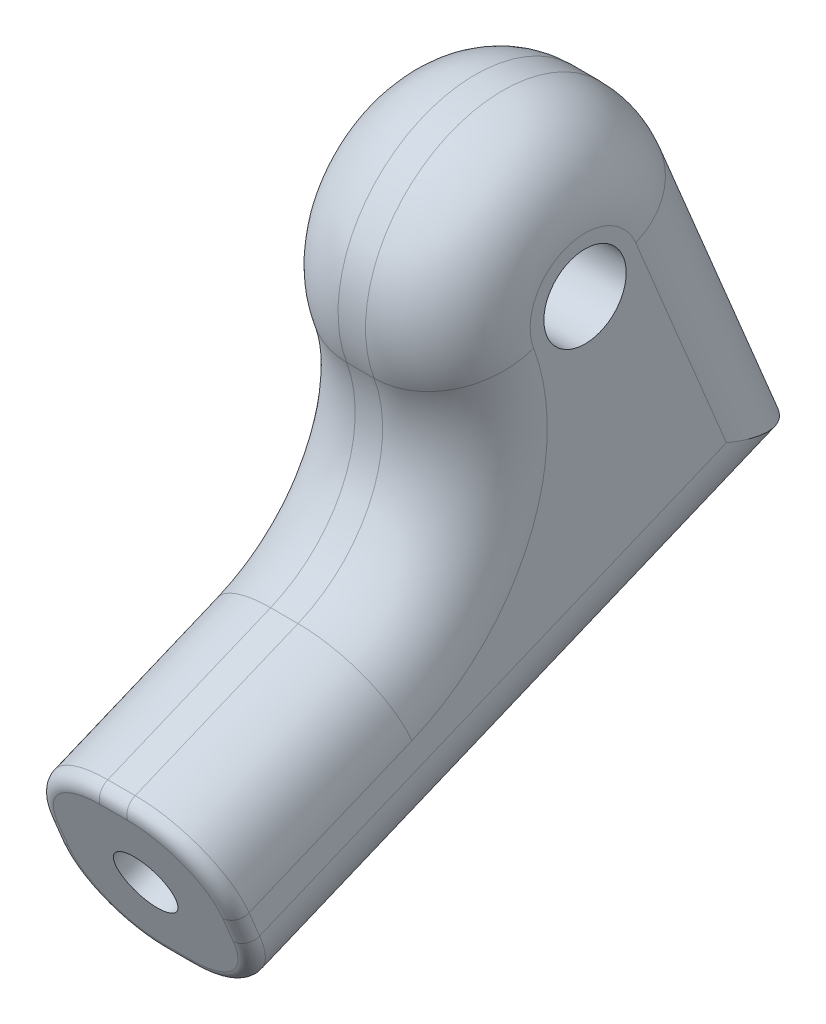
SolidWorks part; units mm, degrees
ref_plane "Front Plane" through (0, 0, 0) normal (0, 0, 1) x (1, 0, 0)
ref_plane "Top Plane" through (0, 0, 0) normal (0, 1, 0) x (1, 0, 0)
ref_plane "Right Plane" through (0, 0, 0) normal (1, 0, 0) x (0, 0, -1)
sketch "Sketch1" plane through (0, 0, 0) normal (1, 0, 0) x (0, 0, -1)
  line L0 (0, -5) -> (-13.8541, -10.7502)
  line L1 (-13.8541, -10.7502) -> (-11.1706, -17.2155)
  line L2 (-11.1706, -17.2155) -> (9.0718, -8.8137)
  line L3 (4.618, 1.9167) -> (9.0718, -8.8137)
  circle A0 centre (0, 0) radius 1.5
  arc A1 (4.618, 1.9167) -> (0, -5) centre (0, 0) ccw
  dimension "D1" = 3
  dimension "D2" = 10
  dimension "D3" = 15
  dimension "D4" = 90
  dimension "D5" = 7
extrude "Boss-Extrude1" add sketch "Sketch1" along normal blind 7
fillet "Fillet1" radius 5 1 edges at (3.5, -5, 0)
fillet "Fillet2" radius 3 10 edges at (0, -3.4485, -6.8449) (0, 4.6538, 1.8282) (0, -5.4759, 4.7923) (7, -3.4485, -6.8449) (7, 4.6538, 1.8282) (7, -5.4759, 4.7923) (0, -9.4231, 10.6565) (0, -13.0146, 1.0494) (7, -9.4231, 10.6565) (7, -13.0146, 1.0494)
sketch "Sketch2" plane through (0, -6.485, 15.6244) normal (0, -0.3833, 0.9236) x (1, 0, 0)
  line L0 (0, -7.618) -> (0, -8.618) construction
  line L1 (4, -4.618) -> (3, -4.618) construction
  circle A0 centre (3.5, -8.118) radius 1.1
  point P2 (0, 0)
  point P6 (0, -8.118)
  point P7 (0, 0)
  point P10 (3.5, -4.618)
  dimension "D1" = 2.2
extrude "Cut-Extrude1" cut sketch "Sketch2" against normal through all
sketch "Sketch3" plane through (0, 0, 0) normal (-1, 0, 0) x (0, 0, 1)
  line L0 (11.1706, -17.2155) -> (-9.0718, -8.8137) construction
  line L1 (2.3853, 1.8276) -> (-0.3901, 2.9796)
  line L2 (-0.3901, 2.9796) -> (-2.7754, 1.152)
  line L3 (-2.7754, 1.152) -> (-2.3853, -1.8276)
  line L4 (-2.3853, -1.8276) -> (0.3901, -2.9796)
  line L5 (0.3901, -2.9796) -> (2.7754, -1.152)
  line L6 (2.7754, -1.152) -> (2.3853, 1.8276)
  circle A0 centre (0, 0) radius 2.6024 construction
  dimension "D1" = 6.01
extrude "Cut-Extrude2" cut sketch "Sketch3" against normal blind 2.2
fillet "Fillet3" radius 0.5 8 edges at (3.5, -10.7502, 13.8541) (6.1213, -11.5618, 13.5172) (7, -13.9828, 12.5123) (6.1213, -16.4039, 11.5075) (3.5, -17.2155, 11.1706) (0.8787, -16.4039, 11.5075) (0, -13.9828, 12.5123) (0.8787, -11.5618, 13.5172)
